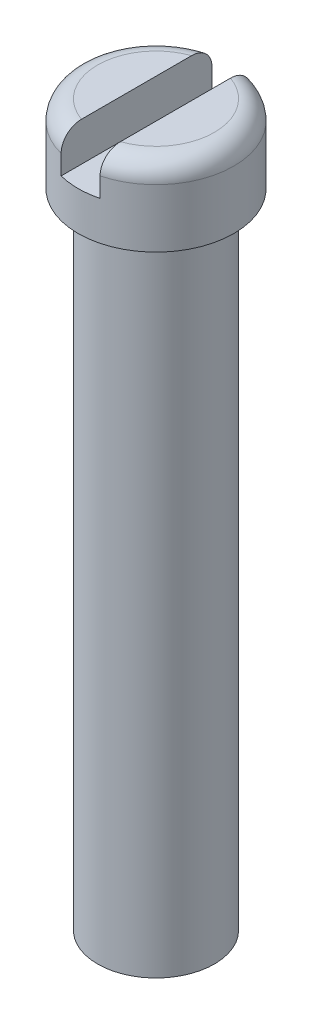
SolidWorks part; units mm, degrees
material "Laiton"
ref_plane "Plan de face" through (0, 0, 0) normal (0, 0, 1) x (1, 0, 0)
ref_plane "Plan de dessus" through (0, 0, 0) normal (0, 1, 0) x (1, 0, 0)
ref_plane "Plan de droite" through (0, 0, 0) normal (1, 0, 0) x (0, 0, -1)
sketch "Esquisse1" plane through (0, 0, 0) normal (0, 1, 0) x (1, 0, 0)
  circle A0 centre (0, 0) radius 1.5
  dimension "D1" = 3
extrude "Boss.-Extru.1" add sketch "Esquisse1" along normal blind 16.5
sketch "Esquisse2" plane through (0, 16.5, 0) normal (0, 1, 0) x (1, 0, 0)
  circle A0 centre (0, 0) radius 2
  dimension "D1" = 4
extrude "Boss.-Extru.2" add sketch "Esquisse2" along normal blind 2
sketch "Esquisse3" plane through (0, 18.5, 0) normal (0, 1, 0) x (1, 0, 0)
  line L1 (-0.5, 2) -> (0.5, 2)
  line L2 (-0.5, 2) -> (-0.5, -2)
  line L3 (-0.5, -2) -> (0.5, -2)
  line L4 (0.5, 2) -> (0.5, -2)
  circle A0 centre (0, 0) radius 2 construction
  dimension "D1" = 2
  dimension "D2" = 2
  dimension "D3" = 1
  dimension "D4" = 0.5
extrude "Enlèv. mat.-Extru.1" cut sketch "Esquisse3" against normal blind 1
fillet "Congé1" radius 0.5 2 edges at (2, 18.5, 0) (-2, 18.5, 0)
